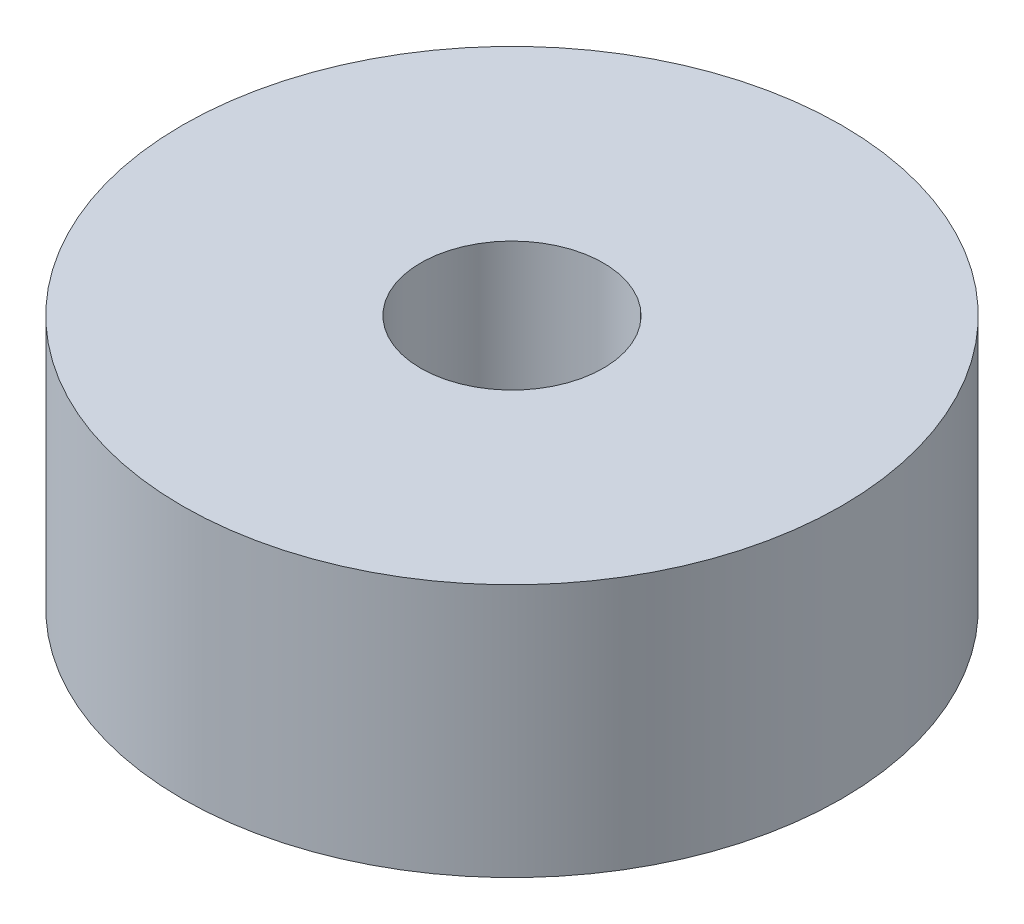
SolidWorks part; units mm, degrees
ref_plane "Спереди" through (0, 0, 0) normal (0, 0, 1) x (1, 0, 0)
ref_plane "Сверху" through (0, 0, 0) normal (0, 1, 0) x (1, 0, 0)
ref_plane "Справа" through (0, 0, 0) normal (1, 0, 0) x (0, 0, -1)
sketch "Эскиз1" plane through (0, 0, 0) normal (0, 1, 0) x (1, 0, 0)
  circle A0 centre (0, 0) radius 6.5
  circle A1 centre (0, 0) radius 1.8
  dimension "D1" = 13
  dimension "D2" = 3.6
extrude "Бобышка-Вытянуть1" add sketch "Эскиз1" along normal blind 5
